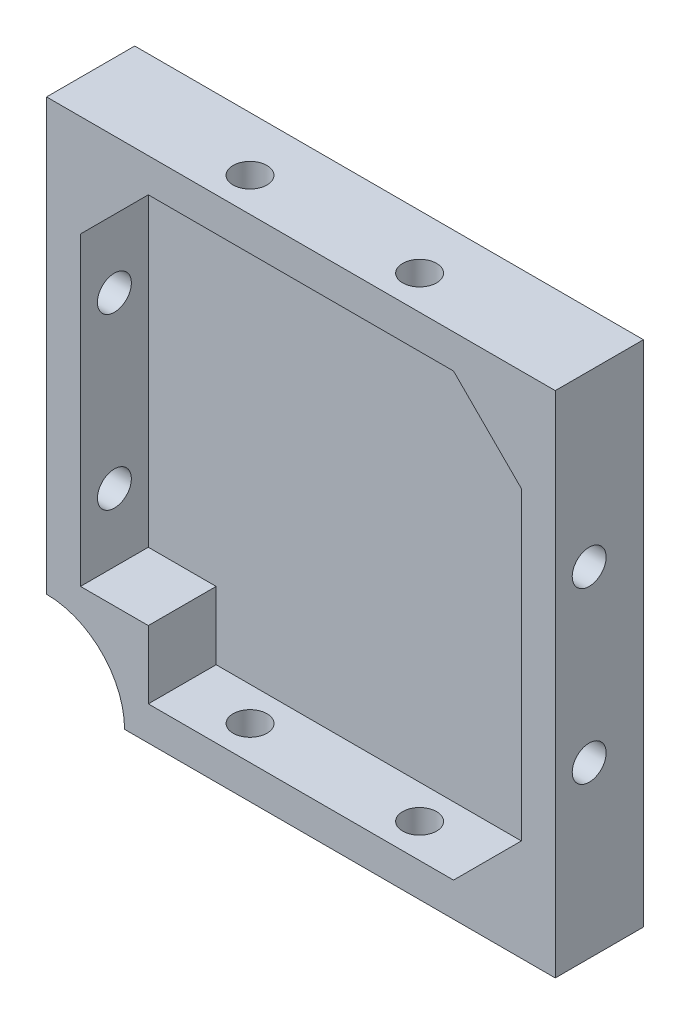
SolidWorks part; units mm, degrees
ref_plane "Plan de face" through (0, 0, 0) normal (0, 0, 1) x (1, 0, 0)
ref_plane "Plan de dessus" through (0, 0, 0) normal (0, 1, 0) x (1, 0, 0)
ref_plane "Plan de droite" through (0, 0, 0) normal (1, 0, 0) x (0, 0, -1)
sketch "Esquisse1" plane through (0, 0, 0) normal (0, 0, 1) x (1, 0, 0)
  line L0 (44.1184, 33.7284) -> (54.1184, 33.7284)
  line L1 (-20.8816, 33.7284) -> (44.1184, 33.7284)
  line L2 (-20.8816, 33.7284) -> (-20.8816, -41.2716)
  line L3 (-20.8816, -41.2716) -> (54.1184, -41.2716)
  line L4 (54.1184, 23.7284) -> (54.1184, -41.2716)
  line L5 (54.1184, 33.7284) -> (54.1184, 23.7284)
  point P6 (54.1184, 33.7284)
  dimension "D1" = 75
  dimension "D2" = 75
extrude "Boss.-Extru.1" add sketch "Esquisse1" along normal blind 13
shell "Coque1" thickness 5
sketch "Esquisse2" plane through (-20.8816, 0, 0) normal (-1, 0, 0) x (0, 0, 1)
  line L0 (13, 33.7284) -> (13, -41.2716) construction
  line L1 (13, 33.7284) -> (0, 33.7284) construction
  line L2 (13, -41.2716) -> (0, -41.2716) construction
  circle A0 centre (8, 8.7284) radius 2.5
  circle A1 centre (8, -16.2716) radius 2.5
  dimension "D1" = 5
  dimension "D2" = 5
  dimension "D3" = 5
  dimension "D4" = 5
  dimension "D5" = 25
  dimension "D6" = 25
extrude "Enlèv. mat.-Extru.1" cut sketch "Esquisse2" against normal up to surface (75 mm away) contours A1 | A0 up to face at (54.1184, -3.7716, 6.5)
sketch "Esquisse3" plane through (0, -41.2716, 0) normal (0, -1, 0) x (1, 0, 0)
  line L0 (-20.8816, 13) -> (54.1184, 13) construction
  line L2 (54.1184, 13) -> (54.1184, 0) construction
  line L3 (-20.8816, 13) -> (-20.8816, 0) construction
  circle A0 centre (4.1184, 8) radius 2.5
  circle A1 centre (29.1184, 8) radius 2.5
  dimension "D1" = 5
  dimension "D2" = 5
  dimension "D3" = 5
  dimension "D4" = 5
  dimension "D5" = 25
  dimension "D6" = 25
extrude "Enlèv. mat.-Extru.2" cut sketch "Esquisse3" against normal up to surface (75 mm away) up to face at (16.6184, 33.7284, 6.5)
sketch "Esquisse4" plane through (0, 0, 3) normal (0, 0, 1) x (1, 0, 0)
  line L0 (-5.8816, 28.7284) -> (-15.8816, 18.7284)
  line L1 (49.1184, 28.7284) -> (-15.8816, 28.7284) construction
  line L2 (-15.8816, 28.7284) -> (-15.8816, -36.2716) construction
  line L3 (-15.8816, 18.7284) -> (-15.8816, 28.7284)
  line L4 (-15.8816, 28.7284) -> (-5.8816, 28.7284)
  line L5 (49.1184, 28.7284) -> (49.1184, 18.7284)
  line L6 (49.1184, -36.2716) -> (49.1184, 28.7284) construction
  line L7 (49.1184, 18.7284) -> (39.1184, 28.7284)
  line L8 (39.1184, 28.7284) -> (49.1184, 28.7284)
  line L9 (49.1184, 28.7284) -> (-15.8816, 28.7284) construction
  line L10 (49.1184, -36.2716) -> (49.1184, -26.2716)
  line L11 (49.1184, -26.2716) -> (39.1184, -36.2716)
  line L12 (-15.8816, -36.2716) -> (49.1184, -36.2716) construction
  line L13 (39.1184, -36.2716) -> (49.1184, -36.2716)
  line L14 (-20.8816, -26.2716) -> (-5.8816, -26.2716)
  line L15 (-20.8816, -41.2716) -> (54.1184, -41.2716) construction
  line L16 (-5.8816, -26.2716) -> (-5.8816, -41.2716)
  line L17 (-5.8816, -41.2716) -> (-20.8816, -41.2716)
  line L18 (-20.8816, -41.2716) -> (-20.8816, -26.2716)
  line L19 (-20.8816, 33.7284) -> (-20.8816, -41.2716) construction
  dimension "D1" = 10
  dimension "D2" = 10
  dimension "D3" = 10
  dimension "D4" = 10
  dimension "D5" = 10
  dimension "D6" = 10
  dimension "D7" = 15
  dimension "D8" = 15
  dimension "D9" = 0
  dimension "D10" = 0
extrude "Boss.-Extru.2" add sketch "Esquisse4" along normal up to surface (10 mm away) up to face at (16.6184, -3.7716, 13)
sketch "Esquisse5" plane through (0, 0, 13) normal (0, 0, 1) x (1, 0, 0)
  circle A0 centre (-20.8816, -41.2716) radius 11.5
  dimension "D1" = 23
extrude "Enlèv. mat.-Extru.3" cut sketch "Esquisse5" against normal up to surface (13 mm away) up to face at (16.6184, -3.7716, 0)
